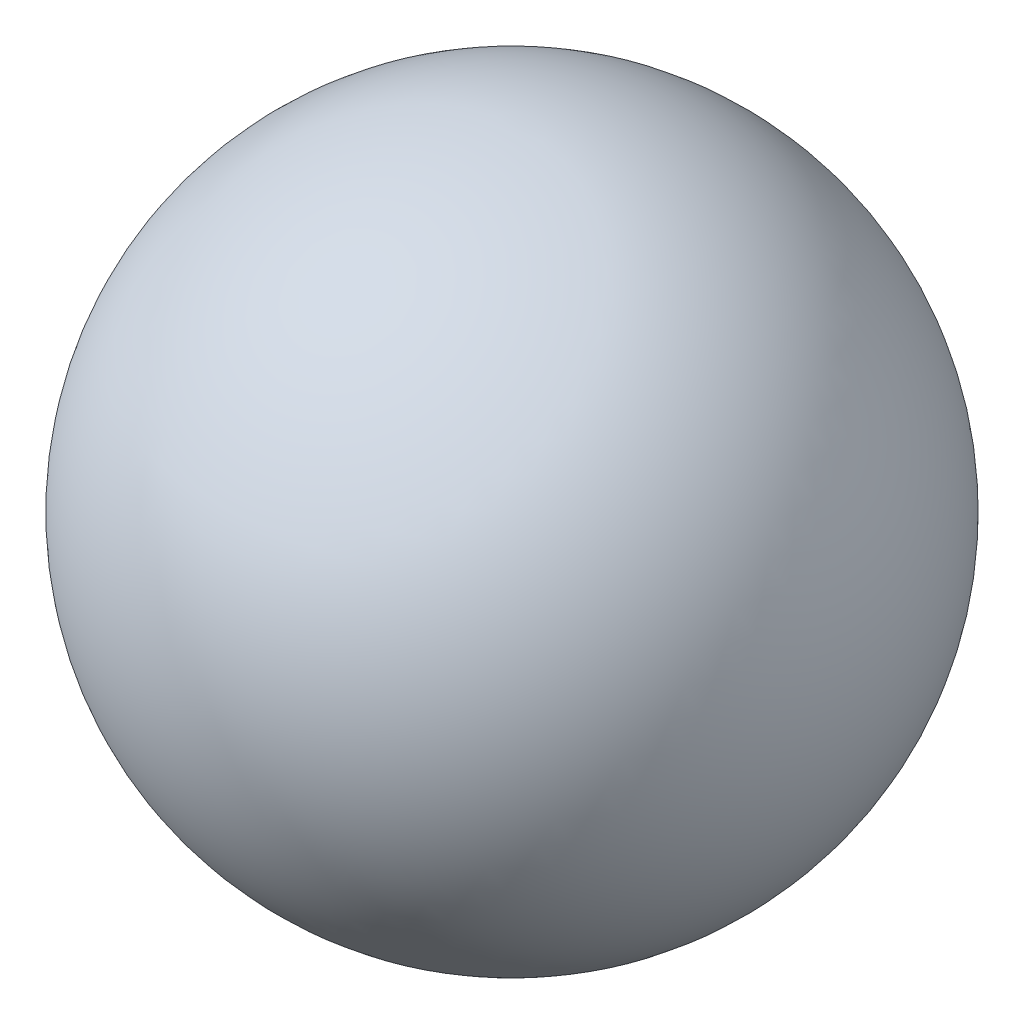
SolidWorks part; units mm, degrees
ref_plane "Front Plane" through (0, 0, 0) normal (0, 0, 1) x (1, 0, 0)
ref_plane "Top Plane" through (0, 0, 0) normal (0, 1, 0) x (1, 0, 0)
ref_plane "Right Plane" through (0, 0, 0) normal (1, 0, 0) x (0, 0, -1)
sketch "Sketch2" plane through (0, 0, 0) normal (0, 0, 1) x (1, 0, 0)
  line L0 (0, -158.4863) -> (0, 158.4863) construction
  line L1 (0, 15.875) -> (0, 15.3924)
  line L2 (0, -15.3924) -> (0, -15.875)
  arc A0 (0, -15.875) -> (0, 15.875) centre (0, 0) ccw
  arc A1 (0, -15.3924) -> (0, 15.3924) centre (0, 0) ccw
  circle A2 centre (0, 0) radius 15.875 construction
  circle A3 centre (0, 0) radius 15.3924 construction
  point P4 (0, 0)
  dimension "D2" = 15.875
  dimension "D1" = 0.4826
revolve "Revolve1" add sketch "Sketch2" angle 360 about L0
